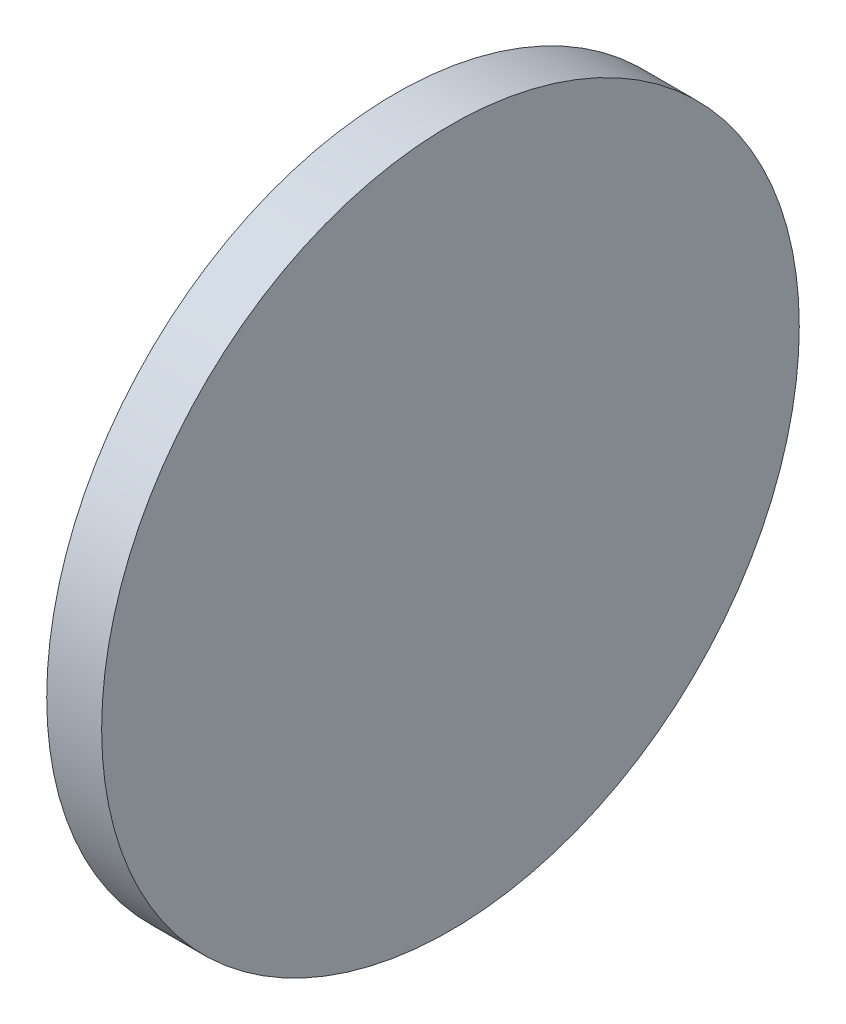
SolidWorks part; units mm, degrees
ref_plane "前视基准面" through (0, 0, 0) normal (0, 0, 1) x (1, 0, 0)
ref_plane "上视基准面" through (0, 0, 0) normal (0, 1, 0) x (1, 0, 0)
ref_plane "右视基准面" through (0, 0, 0) normal (1, 0, 0) x (0, 0, -1)
sketch "草图1" plane through (0, 0, 0) normal (0, 0, 1) x (1, 0, 0)
  line L0 (0, 12.7) -> (0, 0)
  line L2 (0, 12.7) -> (2, 12.7)
  line L3 (0, 0) -> (2, 0)
  line L4 (2, 12.7) -> (2, 0)
  dimension "D1" = 12.7
  dimension "D2" = 2
revolve "旋转2" add sketch "草图1" angle 360 about L3
